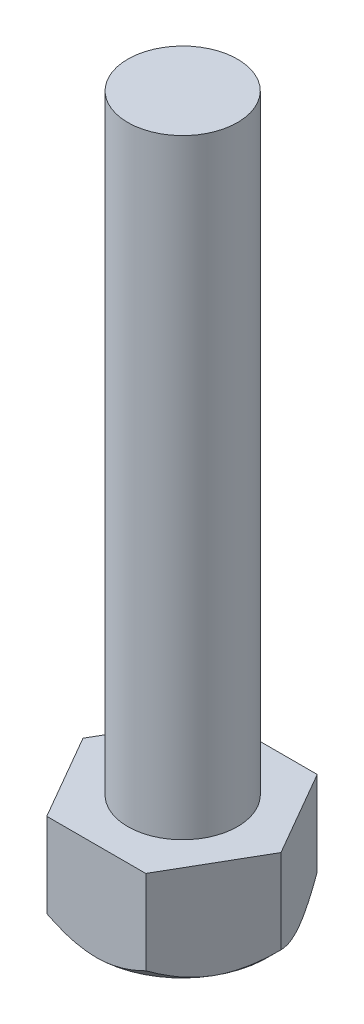
SolidWorks part; units mm, degrees
ref_plane "Front Plane" through (0, 0, 0) normal (0, 0, 1) x (1, 0, 0)
ref_plane "Top Plane" through (0, 0, 0) normal (0, 1, 0) x (1, 0, 0)
ref_plane "Right Plane" through (0, 0, 0) normal (1, 0, 0) x (0, 0, -1)
sketch "Sketch2" plane through (0, 0, 0) normal (0, 0, 1) x (1, 0, 0)
  line L0 (0, 0) -> (0, 25)
  line L1 (0, 25) -> (2.25, 25)
  line L2 (0, 0) -> (2.25, 0)
  line L3 (2.25, 25) -> (2.25, 0) construction
  line L4 (2.25, 25) -> (2.25, 0)
revolve "Revolve1" add sketch "Sketch2" angle 360 about L3
sketch "Sketch3" plane through (0, 0, 0) normal (0, -1, 0) x (1, 0, 0)
  line L2 (6.3084, 0.0273) -> (4.2792, 3.542)
  line L3 (4.2792, 3.542) -> (0.2208, 3.542)
  line L4 (0.2208, 3.542) -> (-1.8084, 0.0273)
  line L5 (-1.8084, 0.0273) -> (0.2208, -3.4874)
  line L6 (0.2208, -3.4874) -> (4.2792, -3.4874)
  line L7 (4.2792, -3.4874) -> (6.3084, 0.0273)
  point P4 (2.25, 0.0273)
extrude "Boss-Extrude1" add sketch "Sketch3" along normal blind 4
sketch "Sketch4" plane through (0, -4, 0) normal (0, -1, 0) x (-1, 0, 0)
  circle A0 centre (-2.25, -0.0273) radius 3.5147
extrude "Cut-Extrude1" cut sketch "Sketch4" against normal through all draft 45 flip side to cut
